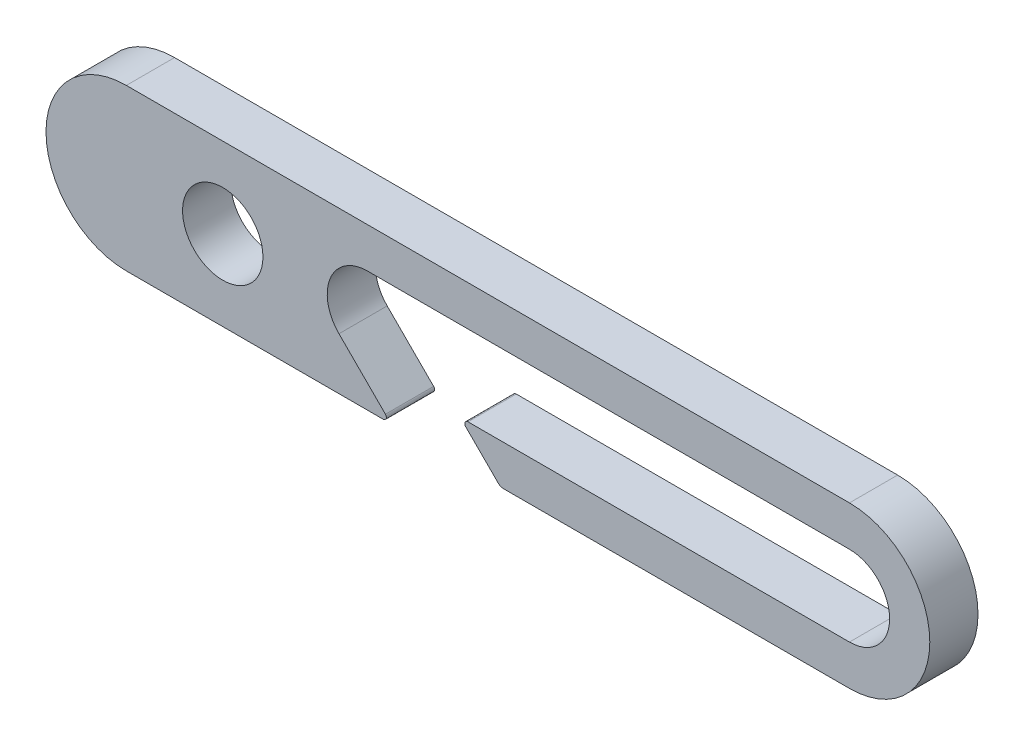
SolidWorks part; units mm, degrees
ref_plane "Front Plane" through (0, 0, 0) normal (0, 0, 1) x (1, 0, 0)
ref_plane "Top Plane" through (0, 0, 0) normal (0, 1, 0) x (1, 0, 0)
ref_plane "Right Plane" through (0, 0, 0) normal (1, 0, 0) x (0, 0, -1)
sketch "Sketch2" plane through (0, 0, 0) normal (0, 0, 1) x (1, 0, 0)
  line L0 (7.7704, 0.8557) -> (54.3236, 0.8557) construction
  line L1 (16.7704, 3.3557) -> (46.7704, 3.3557)
  line L2 (23.0339, -1.6443) -> (46.7704, -1.6443)
  line L3 (1.7704, 5.8557) -> (46.7704, 5.8557)
  line L4 (1.7704, -4.1443) -> (17.752, -4.1443)
  line L5 (1.7704, 3.3557) -> (46.7704, 3.3557) construction
  line L6 (1.7704, -1.6443) -> (46.7704, -1.6443) construction
  line L7 (14.2704, 0.8557) -> (46.7704, 0.8557) construction
  line L8 (15.0026, -0.9121) -> (17.8934, -3.8029)
  line L10 (24.9046, -3.9979) -> (22.8924, -1.9858)
  line L12 (25.2581, -4.1443) -> (46.7704, -4.1443)
  line L13 (1.7704, -4.1443) -> (46.7704, -4.1443) construction
  arc A1 (46.7704, -1.6443) -> (46.7704, 3.3557) centre (46.7704, 0.8557) ccw
  arc A2 (46.7704, -4.1443) -> (46.7704, 5.8557) centre (46.7704, 0.8557) ccw
  arc A3 (1.7704, 5.8557) -> (1.7704, -4.1443) centre (1.7704, 0.8557) ccw
  circle A4 centre (7.7704, 0.8557) radius 2.5
  arc A6 (16.7704, 3.3557) -> (15.0026, -0.9121) centre (16.7704, 0.8557) ccw
  arc A7 (1.7704, 3.3557) -> (1.7704, -1.6443) centre (1.7704, 0.8557) ccw construction
  arc A8 (22.8924, -1.9858) -> (23.0339, -1.6443) centre (23.0339, -1.8443) cw
  arc A9 (25.2581, -4.1443) -> (24.9046, -3.9979) centre (25.2581, -3.6443) cw
  arc A10 (17.752, -4.1443) -> (17.8934, -3.8029) centre (17.752, -3.9443) ccw
  point P3 (25, 0)
  point P16 (0, 0)
  point P21 (0, 0)
  point P30 (0, 0)
  point P31 (0, 0)
  point P32 (0, 0)
  point P34 (0, 0)
  point P35 (0, 0)
  point P36 (14.9871, -0.8694)
  point P37 (0, 0)
  dimension "D2" = 30
  dimension "D3" = 45
  dimension "D5" = 5
  dimension "D6" = 2.5
  dimension "D7" = 2.5
  dimension "D8" = 0.2
  dimension "D9" = 0.5
  dimension "D10" = 0.2
  dimension "D1" = 2.5
  dimension "D4" = 6
extrude "Boss-Extrude1" add sketch "Sketch2" along normal blind 3
